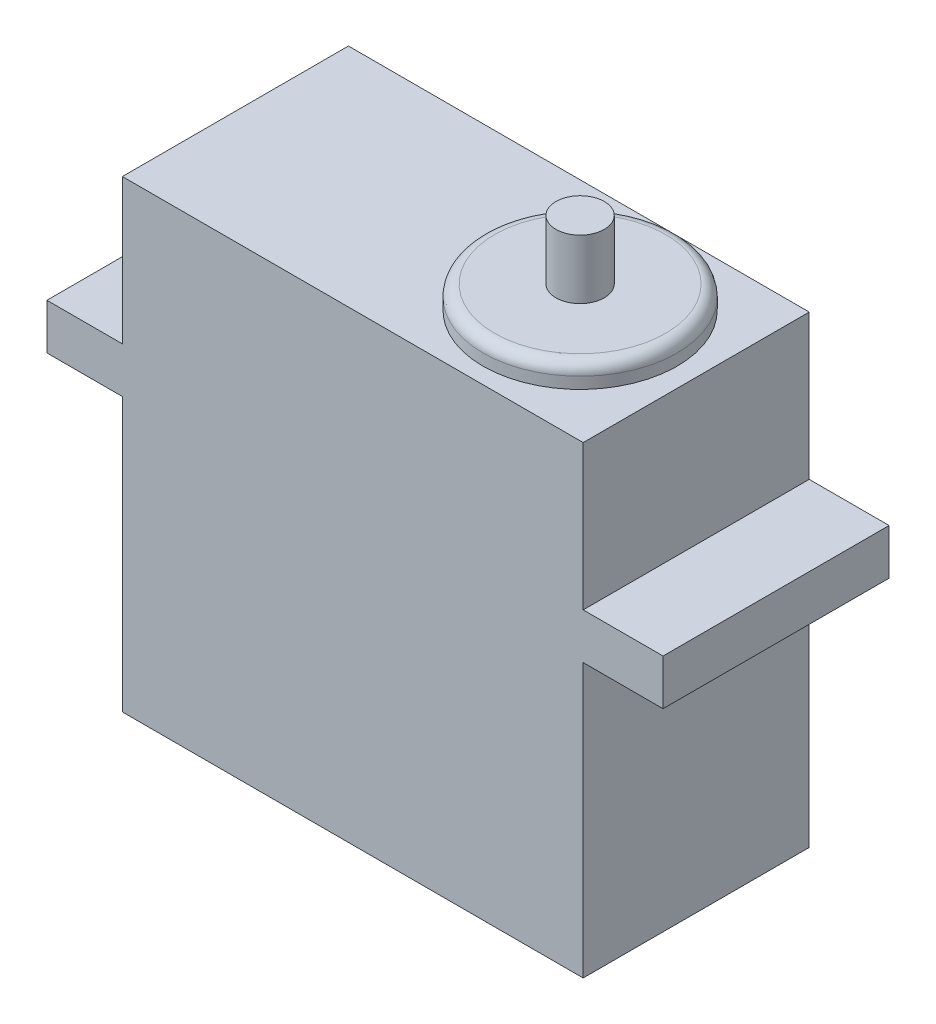
SolidWorks part; units mm, degrees
ref_plane "Front Plane" through (0, 0, 0) normal (0, 0, 1) x (1, 0, 0)
ref_plane "Top Plane" through (0, 0, 0) normal (0, 1, 0) x (1, 0, 0)
ref_plane "Right Plane" through (0, 0, 0) normal (1, 0, 0) x (0, 0, -1)
sketch "Sketch1" plane through (0, 0, 0) normal (0, 1, 0) x (1, 0, 0)
  line L1 (-20.193, 9.906) -> (20.193, 9.906)
  line L2 (-20.193, 9.906) -> (-20.193, -9.906)
  line L3 (-20.193, -9.906) -> (20.193, -9.906)
  line L4 (20.193, 9.906) -> (20.193, -9.906)
  line L5 (-20.193, 9.906) -> (20.193, -9.906) construction
  line L6 (-20.193, -9.906) -> (20.193, 9.906) construction
  point P0 (0, 0)
  dimension "D1" = 19.812
  dimension "D2" = 40.386
extrude "Boss-Extrude1" add sketch "Sketch1" along normal blind 40.64
sketch "Sketch2" plane through (20.193, 0, 0) normal (1, 0, 0) x (0, 0, -1)
  line L0 (-9.906, 40.64) -> (-9.906, 0) construction
  line L1 (-9.906, 27.94) -> (9.906, 27.94)
  line L2 (-9.906, 27.94) -> (-9.906, 23.94)
  line L3 (-9.906, 23.94) -> (9.906, 23.94)
  line L4 (9.906, 27.94) -> (9.906, 23.94)
  line L5 (9.906, 40.64) -> (9.906, 0) construction
  line L7 (-9.906, 0) -> (9.906, 0) construction
  dimension "D1" = 4
  dimension "D2" = 27.94
extrude "Boss-Extrude2" add sketch "Sketch2" along normal blind 7 and the other way blind 47
sketch "Sketch3" plane through (0, 40.64, 0) normal (0, 1, 0) x (1, 0, 0)
  circle A0 centre (10.0186, 0) radius 8.5
  dimension "D1" = 17
extrude "Boss-Extrude3" add sketch "Sketch3" along normal blind 2
fillet "Fillet1" radius 1 1 edges at (10.0186, 42.64, 8.5)
sketch "Sketch4" plane through (0, 42.64, 0) normal (0, 1, 0) x (1, 0, 0)
  circle A0 centre (10.0186, 0) radius 2.1172
extrude "Boss-Extrude4" add sketch "Sketch4" along normal blind 5.2
